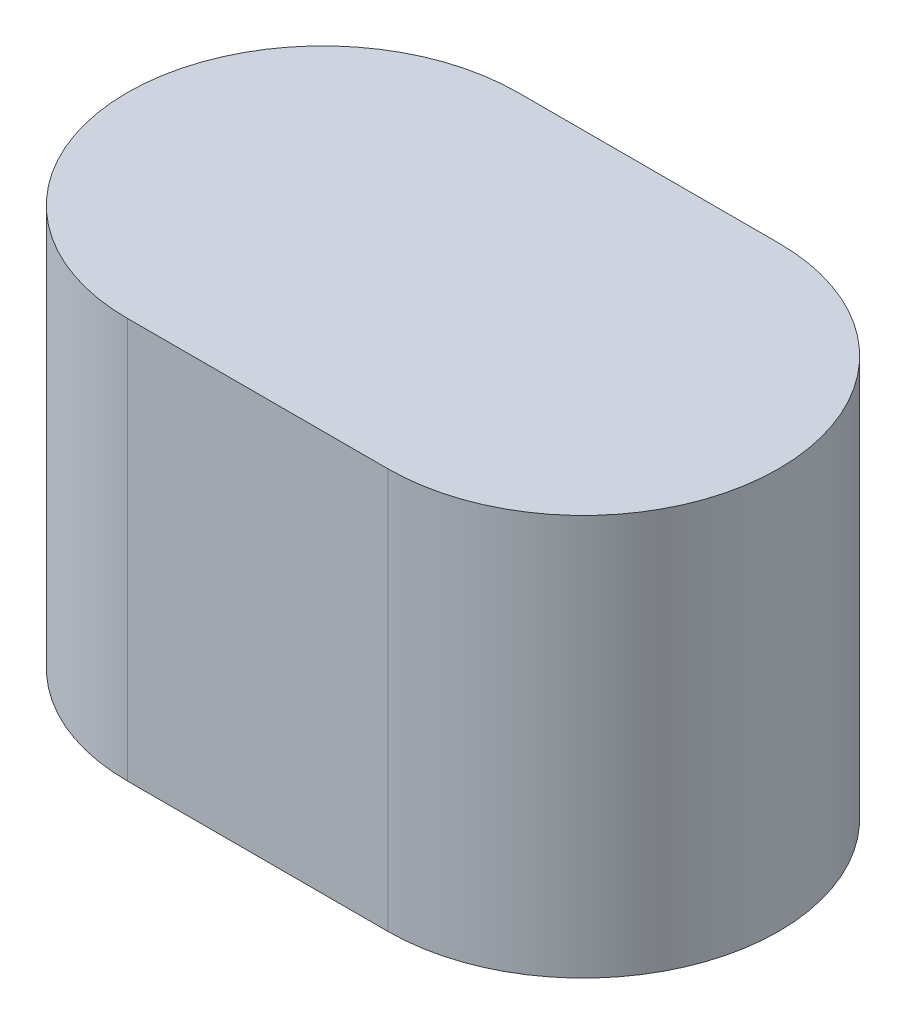
SolidWorks part; units mm, degrees
ref_plane "Front Plane" through (0, 0, 0) normal (0, 0, 1) x (1, 0, 0)
ref_plane "Top Plane" through (0, 0, 0) normal (0, 1, 0) x (1, 0, 0)
ref_plane "Right Plane" through (0, 0, 0) normal (1, 0, 0) x (0, 0, -1)
sketch "Sketch1" plane through (0, 0, 0) normal (0, 1, 0) x (1, 0, 0)
  line L0 (0, 0) -> (4, 0) construction
  line L1 (0, 3) -> (4, 3)
  line L2 (0, -3) -> (4, -3)
  arc A0 (0, 3) -> (0, -3) centre (0, 0) ccw
  arc A1 (4, -3) -> (4, 3) centre (4, 0) ccw
  point P3 (2, 0)
  dimension "D2" = 10
  dimension "D1" = 6
extrude "Boss-Extrude1" add sketch "Sketch1" along normal blind 6.15
